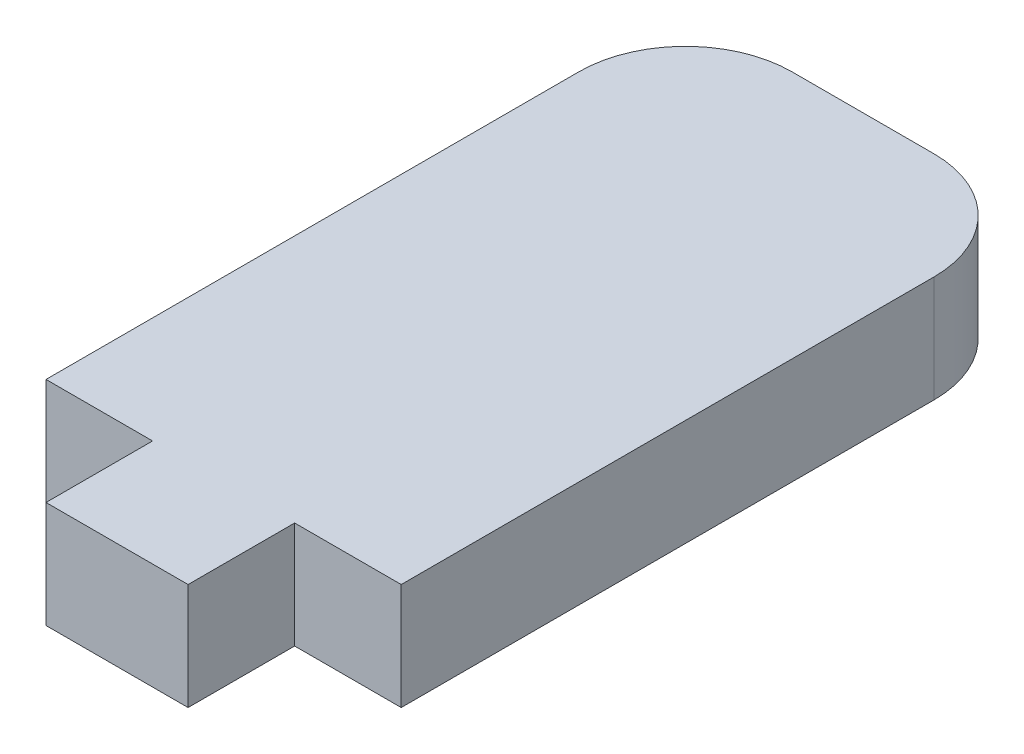
SolidWorks part; units mm, degrees
material "Acrylic (Medium-high impact)"
ref_plane "Plano frontal" through (0, 0, 0) normal (0, 0, 1) x (1, 0, 0)
ref_plane "Plano superior" through (0, 0, 0) normal (0, 1, 0) x (1, 0, 0)
ref_plane "Plano direito" through (0, 0, 0) normal (1, 0, 0) x (0, 0, -1)
sketch "Sketch6" plane through (0, 0, 0) normal (0, 1, 0) x (1, 0, 0)
  line L1 (-2, 10.5) -> (2, 10.5)
  line L2 (-5, 7.5) -> (-5, -7.5)
  line L3 (-5, -7.5) -> (5, -7.5)
  line L4 (5, 7.5) -> (5, -7.5)
  arc A0 (2, 10.5) -> (5, 7.5) centre (2, 7.5) cw
  arc A1 (-2, 10.5) -> (-5, 7.5) centre (-2, 7.5) ccw
  point P4 (0, 10.5)
  point P6 (-5, 0)
  point P9 (5, 10.5)
  point P12 (-5, 10.5)
  dimension "D3" = 3
  dimension "D1" = 10
  dimension "D2" = 18
extrude "Boss-Extrude4" add sketch "Sketch6" along normal mid plane 3
sketch "Sketch8" plane through (0, 0, 0) normal (0, 1, 0) x (1, 0, 0)
  line L5 (-5, -7.5) -> (5, -7.5) construction
  line L6 (-2, -7.5) -> (2, -7.5)
  line L7 (-2, -7.5) -> (-2, -10.5)
  line L8 (-2, -10.5) -> (2, -10.5)
  line L9 (2, -7.5) -> (2, -10.5)
  point P14 (0, -7.5)
  dimension "D1" = 3
  dimension "D3" = 4
extrude "Boss-Extrude5" add sketch "Sketch8" along normal mid plane 3
